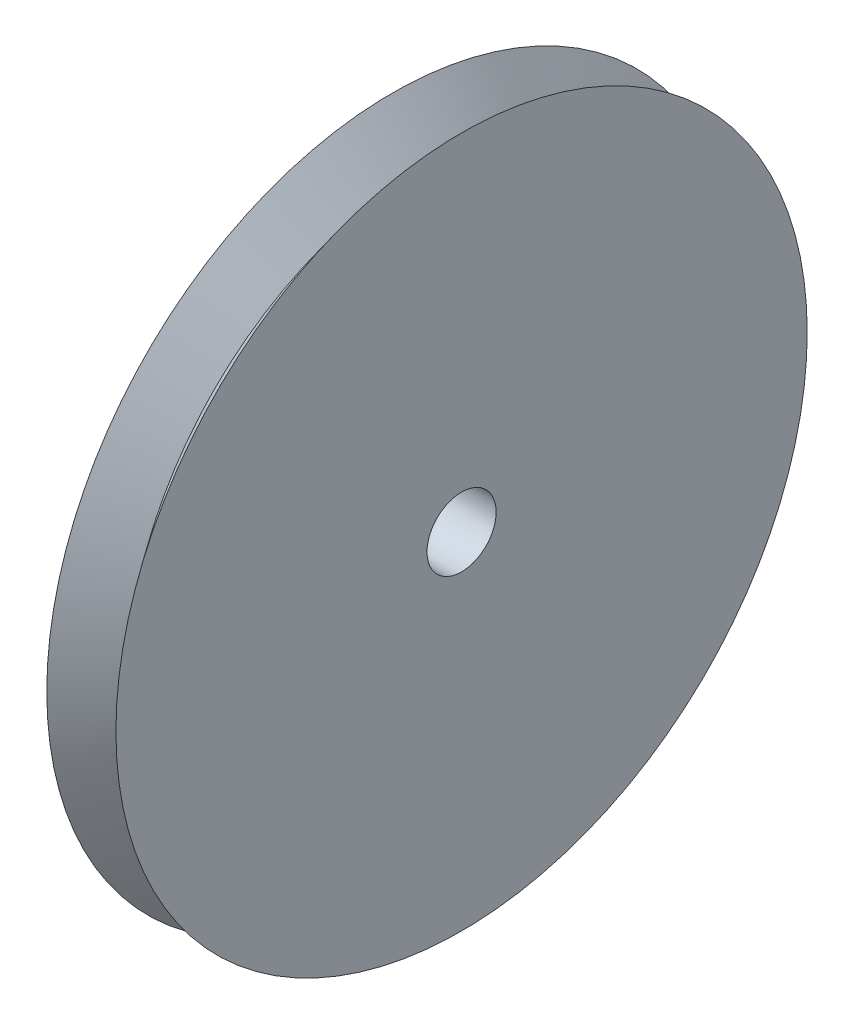
SolidWorks part; units mm, degrees
ref_plane "Front Plane" through (0, 0, 0) normal (0, 0, 1) x (1, 0, 0)
ref_plane "Top Plane" through (0, 0, 0) normal (0, 1, 0) x (1, 0, 0)
ref_plane "Right Plane" through (0, 0, 0) normal (1, 0, 0) x (0, 0, -1)
sketch "Sketch1" plane through (0, 0, 0) normal (0, 1, 0) x (1, 0, 0)
  line L0 (0, 25.4) -> (2.54, 22.098)
  line L1 (0, 0) -> (5.08, 0)
  line L2 (0, 0) -> (0, 25.4)
  line L3 (0, 25.4) -> (5.08, 25.4)
  line L4 (5.08, 0) -> (5.08, 25.4)
  line L5 (2.54, 22.098) -> (5.08, 25.4)
  dimension "D1" = 25.4
  dimension "D2" = 3.302
  dimension "D3" = 5.08
  dimension "D4" = 2.54
revolve "Revolve1" add sketch "Sketch1" angle 360 about L1
sketch "Sketch2" plane through (5.08, 0, 0) normal (1, 0, 0) x (0, 0, -1)
  circle A0 centre (0, 0) radius 2.54
  dimension "D1" = 5.08
extrude "Cut-Extrude1" cut sketch "Sketch2" against normal through all
